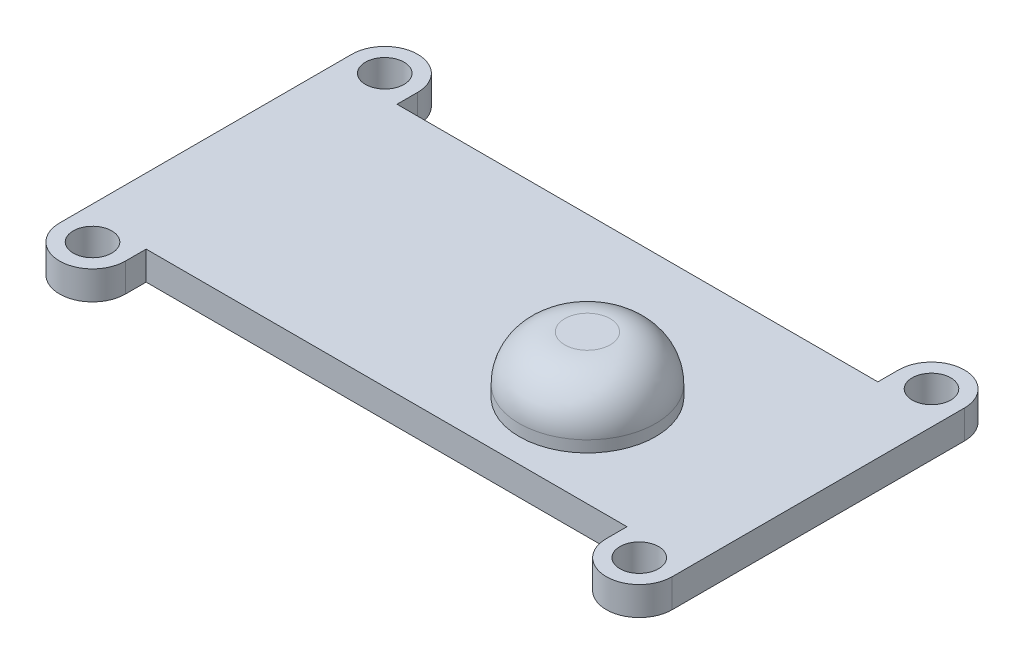
SolidWorks part; units mm, degrees
ref_plane "Front Plane" through (0, 0, 0) normal (0, 0, 1) x (1, 0, 0)
ref_plane "Top Plane" through (0, 0, 0) normal (0, 1, 0) x (1, 0, 0)
ref_plane "Right Plane" through (0, 0, 0) normal (1, 0, 0) x (0, 0, -1)
other "Bounding Box"
ref_plane "Default Plane" through (13.8565, 3.175, 6.7999) normal (0, -1, 0) x (-1, 0, 0)
sketch "Sketch1" plane through (0, 0, 0) normal (0, 1, 0) x (1, 0, 0)
  line L0 (-16.3576, 8.1661) -> (-17.1196, 8.1661) construction
  line L1 (-13.4366, -7.0104) -> (13.4366, -7.0104)
  line L2 (-17.1196, -7.0104) -> (-17.1196, 7.0104)
  line L3 (-17.1196, 7.0104) -> (-15.2781, 7.0104) construction
  line L4 (17.1196, -7.0104) -> (17.1196, 7.0104)
  line L5 (-17.1196, -7.0104) -> (17.1196, 7.0104) construction
  line L6 (-17.1196, 7.0104) -> (17.1196, -7.0104) construction
  line L7 (-17.1196, 7.0104) -> (-17.1196, 8.1661)
  line L8 (-13.4366, 8.1661) -> (-13.4366, 7.0104)
  line L9 (-15.2781, 10.0076) -> (-15.2781, 0) construction
  line L10 (-15.2781, 7.0104) -> (-13.4366, 7.0104) construction
  line L11 (-13.4366, 7.0104) -> (13.4366, 7.0104)
  line L12 (-15.2781, 0) -> (0, 0) construction
  line L13 (-17.1196, -7.0104) -> (-17.1196, -8.1661)
  line L14 (-13.4366, -8.1661) -> (-13.4366, -7.0104)
  line L15 (-17.1196, -7.0104) -> (-13.4366, -7.0104) construction
  line L16 (0, 0) -> (0, -7.0104) construction
  line L17 (13.4366, 8.1661) -> (13.4366, 7.0104)
  line L18 (17.1196, 7.0104) -> (17.1196, 8.1661)
  line L19 (13.4366, -8.1661) -> (13.4366, -7.0104)
  line L20 (17.1196, -7.0104) -> (17.1196, -8.1661)
  line L21 (13.4366, 7.0104) -> (17.1196, 7.0104) construction
  line L22 (13.4366, -7.0104) -> (17.1196, -7.0104) construction
  circle A0 centre (-15.2781, 8.1661) radius 1.0795
  arc A1 (-17.1196, 8.1661) -> (-13.4366, 8.1661) centre (-15.2781, 8.1661) cw
  arc A2 (-17.1196, -8.1661) -> (-13.4366, -8.1661) centre (-15.2781, -8.1661) ccw
  circle A3 centre (-15.2781, -8.1661) radius 1.0795
  arc A4 (17.1196, 8.1661) -> (13.4366, 8.1661) centre (15.2781, 8.1661) ccw
  circle A5 centre (15.2781, 8.1661) radius 1.0795
  circle A6 centre (15.2781, -8.1661) radius 1.0795
  arc A7 (17.1196, -8.1661) -> (13.4366, -8.1661) centre (15.2781, -8.1661) cw
  point P0 (0, 0)
  dimension "D3" = 2.159
  dimension "D1" = 34.2392
  dimension "D2" = 14.0208
  dimension "D4" = 0.762
  dimension "D5" = 10.0076
extrude "Boss-Extrude1" add sketch "Sketch1" along normal mid plane 1.6002
sketch "Sketch2" plane through (0, 0.8001, 0) normal (0, 1, 0) x (1, 0, 0)
  line L0 (2.2606, -1.8542) -> (17.1196, -1.8542) construction
  line L1 (17.1196, -8.1661) -> (17.1196, 8.1661) construction
  line L2 (6.0706, 1.9558) -> (6.0706, -7.0104) construction
  line L3 (-13.4366, -7.0104) -> (13.4366, -7.0104) construction
  circle A0 centre (6.0706, -1.8542) radius 3.81
  dimension "D1" = 7.62
  dimension "D2" = 14.859
  dimension "D3" = 8.9662
extrude "Boss-Extrude2" add sketch "Sketch2" along normal blind 3.175
fillet "Fillet1" radius 2.54 1 edges at (6.0706, 3.9751, 5.6642)
